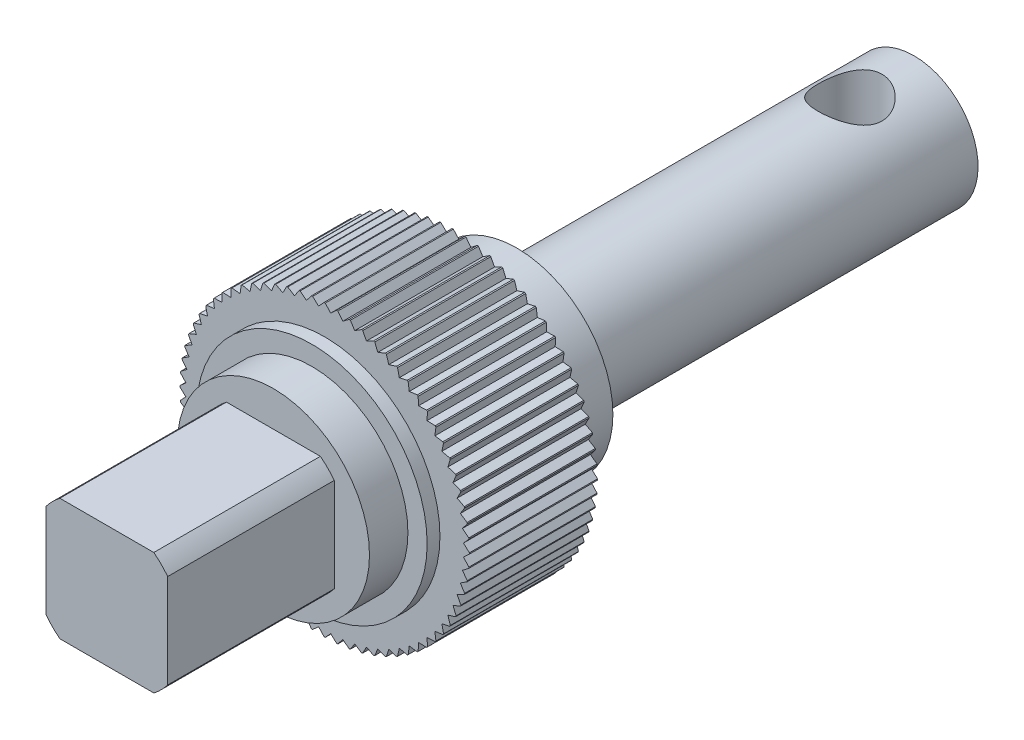
SolidWorks part; units mm, degrees
ref_plane "前视基准面" through (0, 0, 0) normal (0, 0, 1) x (1, 0, 0)
ref_plane "上视基准面" through (0, 0, 0) normal (0, 1, 0) x (1, 0, 0)
ref_plane "右视基准面" through (0, 0, 0) normal (1, 0, 0) x (0, 0, -1)
sketch "草图1" plane through (0, 0, 0) normal (0, 0, 1) x (1, 0, 0)
  circle A0 centre (0, 0) radius 10.8
  dimension "D1" = 21.6
extrude "凸台-拉伸1" add sketch "草图1" along normal blind 10
sketch "草图2" plane through (0, 0, 10) normal (0, 0, 1) x (1, 0, 0)
  line L0 (0, 0) -> (0, 11.35) construction
  line L1 (0, 11.35) -> (-0.5153, 10.7877)
  line L2 (-0.5153, 10.7877) -> (0.5153, 10.7877)
  line L3 (0, 11.35) -> (0.5153, 10.7877)
  circle A0 centre (0, 0) radius 10.8 construction
  point P9 (0, 10.7877)
  dimension "D1" = 11.35
  dimension "D2" = 47.5
extrude "凸台-拉伸2" add sketch "草图2" against normal blind 10
pattern_circular "阵列(圆周)1" count 72 over 360 about axis through (0, 0, 0) along (0, 0, 1) of "凸台-拉伸2"
sketch "草图4" plane through (0, 0, 0) normal (1, 0, 0) x (0, 0, -1)
  line L0 (0, 0) -> (-27, 0) construction
  line L1 (-27, 0) -> (-27, 6)
  line L2 (-27, 6) -> (-14, 6)
  line L3 (-14, 6) -> (-14, 7.5)
  line L4 (-14, 7.5) -> (5, 7.5)
  line L5 (5, 7.5) -> (5, 5)
  line L6 (5, 5) -> (36, 5)
  line L7 (36, 5) -> (36, 0)
  line L8 (36, 0) -> (-27, 0)
  dimension "D1" = 5
  dimension "D2" = 7.5
  dimension "D3" = 5
  dimension "D4" = 6
  dimension "D5" = 27
  dimension "D6" = 14
  dimension "D7" = 31
revolve "旋转1" add sketch "草图4" angle 360 about L0
sketch "草图6" plane through (0, 0, 0) normal (0, 1, 0) x (1, 0, 0)
  line L0 (5, 36) -> (-5, 36) construction
  circle A0 centre (0, 31) radius 2.5
  dimension "D1" = 5
  dimension "D2" = 5
extrude "切除-拉伸1" cut sketch "草图6" against normal mid plane 10
sketch "草图7" plane through (0, 0, 14) normal (0, 0, 1) x (1, 0, 0)
  line L1 (4.75, -4.75) -> (-4.75, -4.75)
  line L2 (4.75, -4.75) -> (4.75, 4.75)
  line L3 (4.75, 4.75) -> (-4.75, 4.75)
  line L4 (-4.75, -4.75) -> (-4.75, 4.75)
  line L5 (4.75, -4.75) -> (-4.75, 4.75) construction
  line L6 (4.75, 4.75) -> (-4.75, -4.75) construction
  point P0 (0, 0)
  dimension "D1" = 9.5
  dimension "D2" = 9.5
extrude "切除-拉伸2" cut sketch "草图7" along normal blind 20 flip side to cut
sketch "草图8" plane through (0, 0, 10) normal (0, 0, 1) x (1, 0, 0)
  circle A0 centre (0, 0) radius 9
  dimension "D1" = 18
extrude "凸台-拉伸3" add sketch "草图8" along normal blind 1
sketch "草图10" plane through (0, 0, 10) normal (0, 0, 1) x (1, 0, 0)
  circle A0 centre (0, 0) radius 16.6588
  circle A1 centre (0, 0) radius 11.3
extrude "切除-拉伸4" cut sketch "草图10" against normal through all
equation "\"9。5\"=9.63954"
